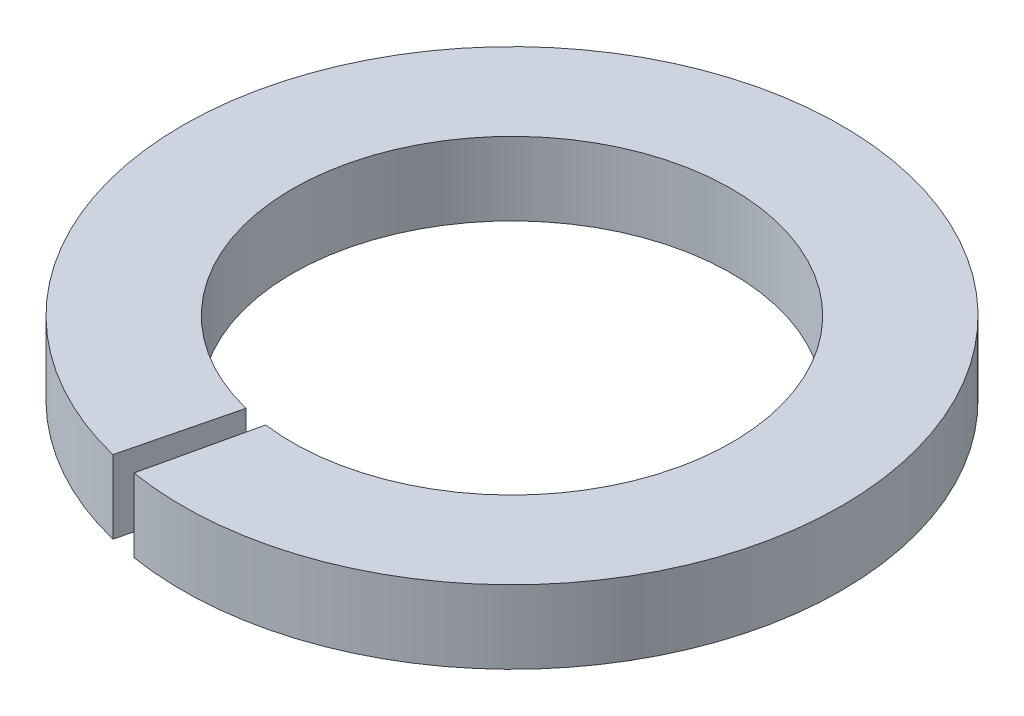
SolidWorks part; units mm, degrees
ref_plane "Спереди" through (0, 0, 0) normal (0, 0, 1) x (1, 0, 0)
ref_plane "Сверху" through (0, 0, 0) normal (0, 1, 0) x (1, 0, 0)
ref_plane "Справа" through (0, 0, 0) normal (1, 0, 0) x (0, 0, -1)
sketch "Эскиз1" plane through (0, 0, 0) normal (0, 1, 0) x (1, 0, 0)
  line L0 (-0.7215, -2.912) -> (-1.0822, -4.3679)
  line L1 (-0.7215, -4.4418) -> (-0.3897, -2.9746)
  arc A0 (-0.3897, -2.9746) -> (-0.7215, -2.912) centre (0, 0) ccw
  arc A1 (-0.7215, -4.4418) -> (-1.0822, -4.3679) centre (0, 0) ccw
  dimension "D1" = 9
  dimension "D2" = 6
extrude "Бобышка-Вытянуть1" add sketch "Эскиз1" along normal blind 1
